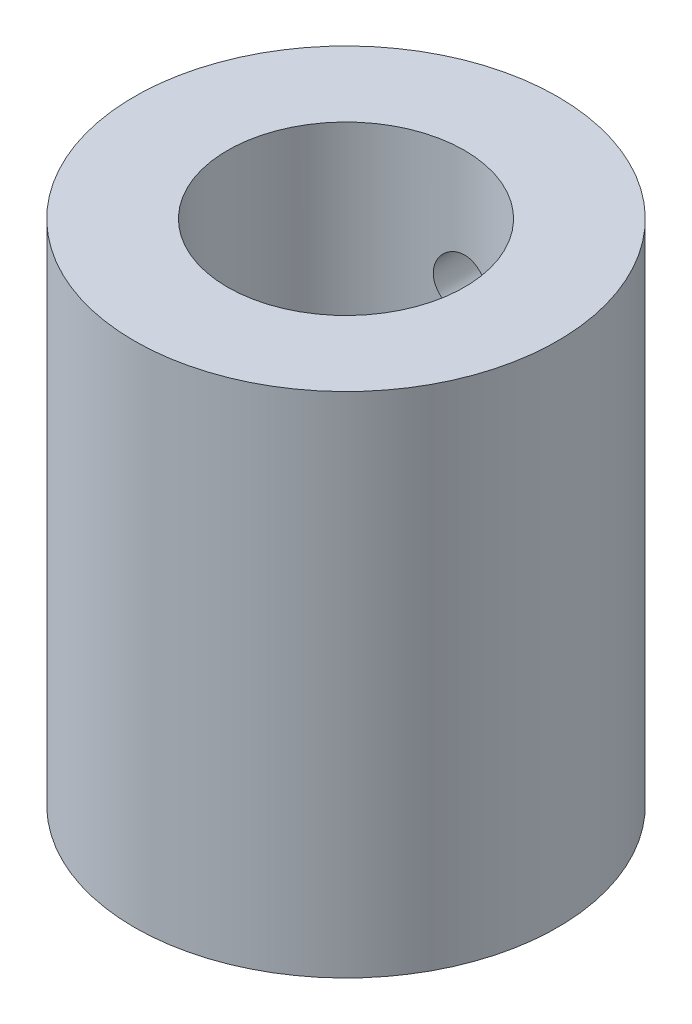
SolidWorks part; units mm, degrees
ref_plane "Front Plane" through (0, 0, 0) normal (0, 0, 1) x (1, 0, 0)
ref_plane "Top Plane" through (0, 0, 0) normal (0, 1, 0) x (1, 0, 0)
ref_plane "Right Plane" through (0, 0, 0) normal (1, 0, 0) x (0, 0, -1)
sketch "Sketch1" plane through (0, 0, 0) normal (0, 1, 0) x (1, 0, 0)
  circle A0 centre (0, 0) radius 12.5
  dimension "D1" = 25
extrude "Boss-Extrude1" add sketch "Sketch1" along normal blind 30
sketch "Sketch2" plane through (0, 30, 0) normal (0, 1, 0) x (1, 0, 0)
  circle A0 centre (0, 0) radius 7
  dimension "D1" = 14
extrude "Cut-Extrude1" cut sketch "Sketch2" against normal blind 23
sketch "Sketch4" plane through (0, 0, 0) normal (0, -1, 0) x (1, 0, 0)
  line L0 (4.7021, -1.7) -> (-4.7021, -1.7) construction
  line L1 (8, 1.8) -> (-8, 1.8)
  line L2 (8, 1.8) -> (8, -1.8)
  line L3 (8, -1.8) -> (-8, -1.8)
  line L4 (-8, 1.8) -> (-8, -1.8)
  line L5 (8, 1.8) -> (-8, -1.8) construction
  line L6 (8, -1.8) -> (-8, 1.8) construction
  arc A0 (4.7021, -1.7) -> (4.7021, 1.7) centre (0, 0) ccw construction
  point P0 (0, 0)
  point P11 (5, 0)
  dimension "D1" = 0.1
  dimension "D2" = 3
extrude "Cut-Extrude2" [suppressed] cut sketch "Sketch4" against normal blind 7.5
fillet "Fillet1" [suppressed] radius 1.5
sketch "Sketch5" plane through (0, 0, 0) normal (0, -1, 0) x (-1, 0, 0)
  line L0 (2.3833, 3.15) -> (8.8034, 3.15)
  line L1 (-8.8034, 3.15) -> (-2.3833, 3.15)
  line L2 (2.3833, -3.15) -> (8.8034, -3.15)
  line L3 (-8.8034, -3.15) -> (-2.3833, -3.15)
  line L5 (-9.1795, 1.7772) -> (9.1795, -1.7772) construction
  line L6 (-16.2701, -3.15) -> (16.2701, 3.15) construction
  arc A0 (-8.8034, 3.15) -> (-8.8034, -3.15) centre (0, 0) ccw
  arc A1 (8.8034, -3.15) -> (8.8034, 3.15) centre (0, 0) ccw
  arc A3 (2.3833, 3.15) -> (-2.3833, 3.15) centre (0, 0) ccw
  arc A5 (-2.3833, -3.15) -> (2.3833, -3.15) centre (0, 0) ccw
  dimension "D1" = 18.7
  dimension "D4" = 3.95
  dimension "D2" = 17.6068
  dimension "D3" = 17.6068
extrude "Cut-Extrude3" cut sketch "Sketch5" against normal blind 7.6
sketch "Sketch6" plane through (0, 0, 0) normal (0, -1, 0) x (1, 0, 0)
  line L0 (-8.8034, 3.15) -> (-5.9651, 0.3117) construction
  line L1 (-2.3833, 3.15) -> (-8.8034, 3.15) construction
  line L2 (0, 0) -> (0, 2.655) construction
  line L3 (0, 0) -> (4.0379, 0) construction
  circle A0 centre (-8.167, 2.5136) radius 1
  circle A1 centre (8.167, 2.5136) radius 1
  circle A2 centre (8.167, -2.5136) radius 1
  circle A3 centre (-8.167, -2.5136) radius 1
  dimension "D1" = 2
  dimension "D2" = 45
  dimension "D3" = 0.9
extrude "Cut-Extrude4" cut sketch "Sketch6" against normal blind 7.6
fillet "Fillet2" radius 1 8 edges at (7.3956, 3.8, -3.15) (9.0991, 3.8, -2.1514) (9.0991, 3.8, 2.1514) (7.3956, 3.8, 3.15) (-7.3956, 3.8, -3.15) (-9.0991, 3.8, -2.1514) (-7.3956, 3.8, 3.15) (-9.0991, 3.8, 2.1514)
sketch "Sketch7" plane through (0, 0, 0) normal (0, 0, 1) x (1, 0, 0)
  line L0 (7, 30) -> (-7, 30) construction
  circle A0 centre (0, 23) radius 1.65
  point P2 (0, 0)
  dimension "D1" = 3.3
  dimension "D2" = 7
extrude "Cut-Extrude5" cut sketch "Sketch7" against normal blind 19.5
